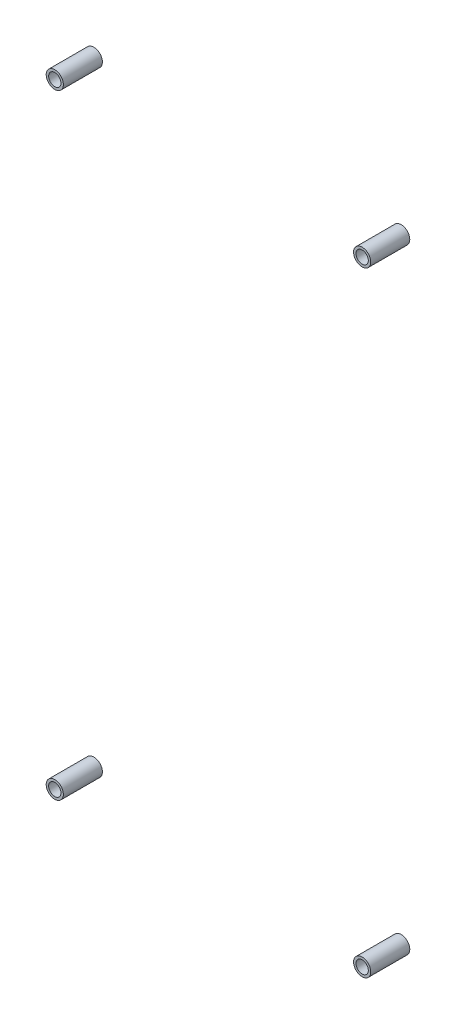
SolidWorks part; units mm, degrees
ref_plane "Front Plane" through (0, 0, 0) normal (0, 0, 1) x (1, 0, 0)
ref_plane "Top Plane" through (0, 0, 0) normal (0, 1, 0) x (1, 0, 0)
ref_plane "Right Plane" through (0, 0, 0) normal (1, 0, 0) x (0, 0, -1)
sketch "Sketch1" plane through (0, 0, 0) normal (0, 0, 1) x (1, 0, 0)
  line L3 (-76.2, 205.74) -> (-76.2, 2.54) construction
  line L6 (-116.2, 180.34) -> (-36.2, 180.34) construction
  circle A0 centre (-116.2, 180.34) radius 2.235
  circle A1 centre (-36.2, 180.34) radius 2.235
  circle A2 centre (-116.2, 20.34) radius 2.235
  circle A3 centre (-36.2, 20.34) radius 2.235
  circle A4 centre (-116.2, 180.34) radius 1.6
  circle A5 centre (-36.2, 180.34) radius 1.6
  circle A6 centre (-36.2, 20.34) radius 1.6
  circle A7 centre (-116.2, 20.34) radius 1.6
  point P18 (-76.2, 154.94)
  point P19 (-76.2, 154.94)
  point P20 (-76.2, 154.94)
  dimension "D3" = 4.47
  dimension "D4" = 3.2
  dimension "D1" = 160
  dimension "D2" = 80
extrude "Boss-Extrude1" add sketch "Sketch1" along normal blind 10.16
